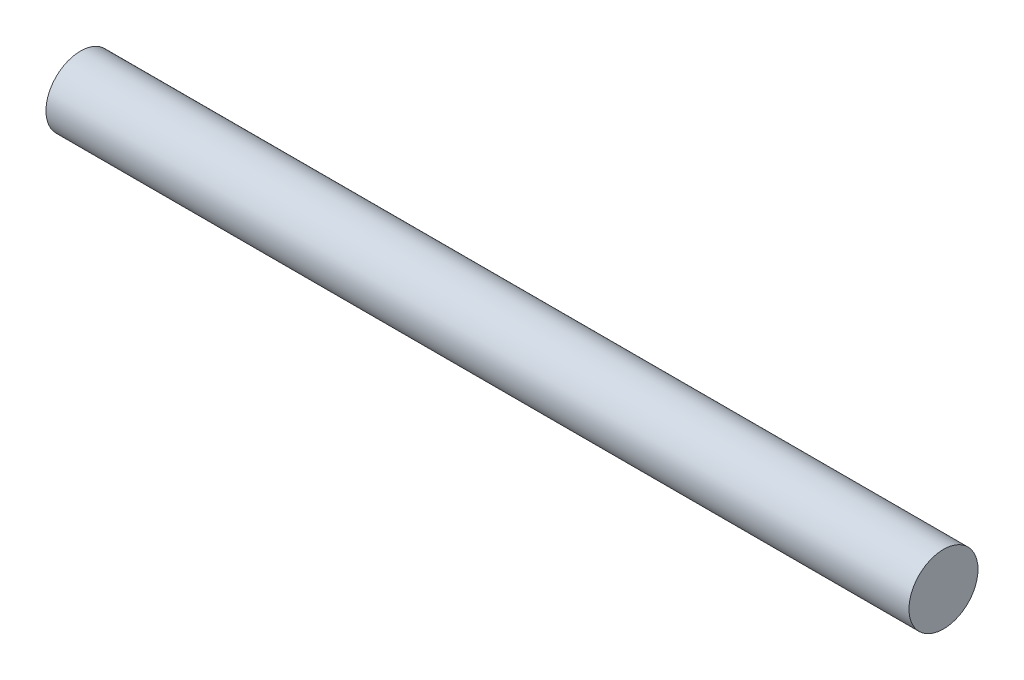
SolidWorks part; units mm, degrees
ref_plane "Front Plane" through (0, 0, 0) normal (0, 0, 1) x (1, 0, 0)
ref_plane "Top Plane" through (0, 0, 0) normal (0, 1, 0) x (1, 0, 0)
ref_plane "Right Plane" through (0, 0, 0) normal (1, 0, 0) x (0, 0, -1)
sketch "Sketch1" plane through (0, 0, 0) normal (1, 0, 0) x (0, 0, -1)
  circle A0 centre (-4.9366, 1.1789) radius 0.8
  dimension "D1" = 1.6
extrude "Boss-Extrude1" add sketch "Sketch1" along normal blind 20
sketch "Sketch2" plane through (0, 0, 0) normal (-1, 0, 0) x (0, 0, 1)
  point P0 (4.9366, 1.1789)
sketch "Sketch3" plane through (20, 0, 0) normal (1, 0, 0) x (0, 0, -1)
  point P0 (-4.9366, 1.1789)
sketch3d "3DSketch1"
  line L0 (20, 1.1789, 4.9366) -> (0, 1.1789, 4.9366) construction
